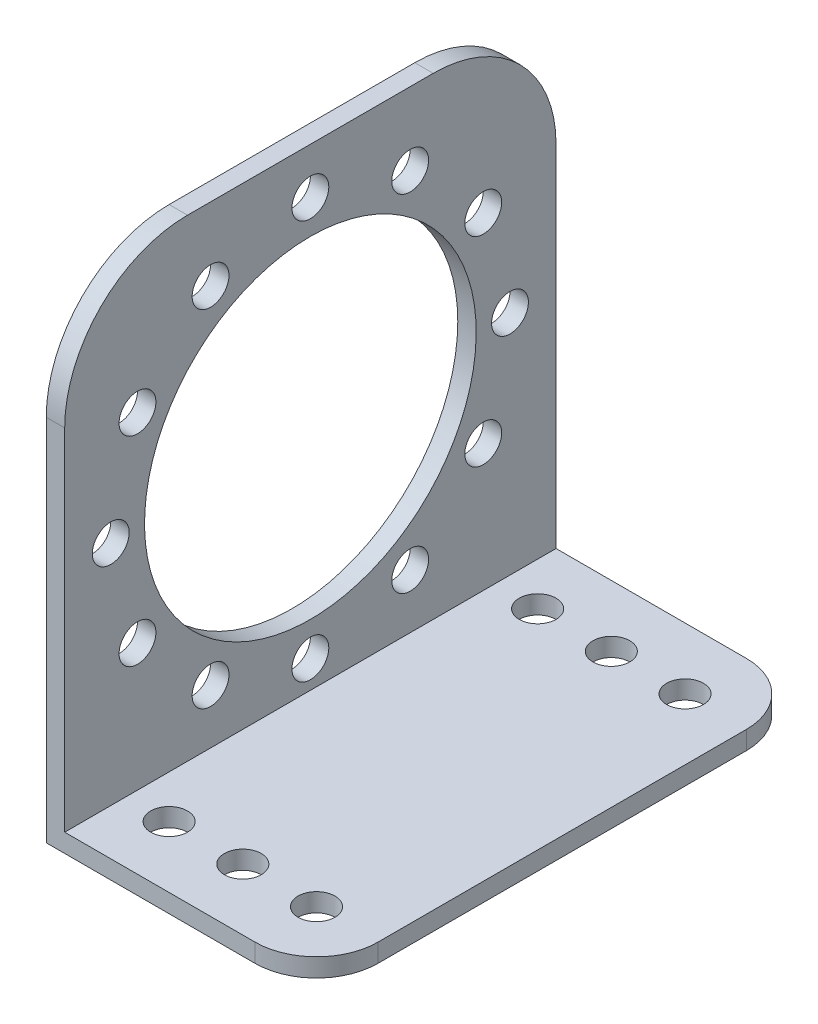
SolidWorks part; units mm, degrees
ref_plane "Front Plane" through (0, 0, 0) normal (0, 0, 1) x (1, 0, 0)
ref_plane "Top Plane" through (0, 0, 0) normal (0, 1, 0) x (1, 0, 0)
ref_plane "Right Plane" through (0, 0, 0) normal (1, 0, 0) x (0, 0, -1)
sketch "Sketch1" plane through (0, 0, 0) normal (0, 0, 1) x (1, 0, 0)
  line L0 (0, 0) -> (22, 0)
  line L1 (0, 0) -> (0, 40)
  line L2 (0, 40) -> (1.5, 40)
  line L3 (1.5, 40) -> (1.5, 1.5)
  line L4 (1.5, 1.5) -> (22, 1.5)
  line L5 (22, 1.5) -> (22, 0)
  dimension "D1" = 40
  dimension "D2" = 22
  dimension "D3" = 1.5
  dimension "D4" = 1.5
extrude "Boss-Extrude1" add sketch "Sketch1" along normal mid plane 40
sketch "Sketch2" plane through (1.5, 0, 0) normal (1, 0, 0) x (0, 0, -1)
  line L0 (-20, 40) -> (20, 40) construction
  circle A0 centre (0, 20) radius 13.5
  dimension "D1" = 27
  dimension "D2" = 20
extrude "Cut-Extrude1" cut sketch "Sketch2" against normal blind 40
sketch "Sketch4" plane through (1.5, 0, 0) normal (1, 0, 0) x (0, 0, -1)
  line L0 (0, 0) -> (0, 20) construction
  line L1 (0, 20) -> (16.25, 20) construction
  circle A1 centre (0, 20) radius 16.25 construction
  circle A2 centre (16.25, 20) radius 1.5
  circle A3 centre (14.0729, 11.875) radius 1.5
  circle A4 centre (8.125, 5.9271) radius 1.5
  circle A5 centre (0, 3.75) radius 1.5
  circle A6 centre (-8.125, 5.9271) radius 1.5
  circle A7 centre (-14.0729, 11.875) radius 1.5
  circle A8 centre (-16.25, 20) radius 1.5
  circle A9 centre (-14.0729, 28.125) radius 1.5
  circle A10 centre (-8.125, 34.0729) radius 1.5
  circle A11 centre (0, 36.25) radius 1.5
  circle A12 centre (8.125, 34.0729) radius 1.5
  circle A13 centre (14.0729, 28.125) radius 1.5
  dimension "D2" = 32.5
  dimension "D3" = 3
  dimension "D1" = 20
  dimension "D5" = 16.25
  dimension "D4" = 12
extrude "Cut-Extrude2" cut sketch "Sketch4" against normal blind 40
sketch "Sketch5" plane through (0, 1.5, 0) normal (0, 1, 0) x (1, 0, 0)
  line L0 (22, 20) -> (1.5, 20) construction
  line L1 (22, -20) -> (22, 20) construction
  line L2 (-12.1, 0) -> (12.1, 0) construction
  circle A0 centre (5, 15) radius 1.5
  circle A1 centre (11, 15) radius 1.5
  circle A2 centre (17, 15) radius 1.5
  circle A3 centre (17, -15) radius 1.5
  circle A4 centre (11, -15) radius 1.5
  circle A5 centre (5, -15) radius 1.5
  dimension "D2" = 3
  dimension "D1" = 5
  dimension "D4" = 5
  dimension "D3" = 3
extrude "Cut-Extrude3" cut sketch "Sketch5" against normal blind 40
fillet "Fillet1" radius 10 2 edges at (0.75, 40, -20) (0.75, 40, 20)
fillet "Fillet2" radius 5 2 edges at (22, 0.75, -20) (22, 0.75, 20)
